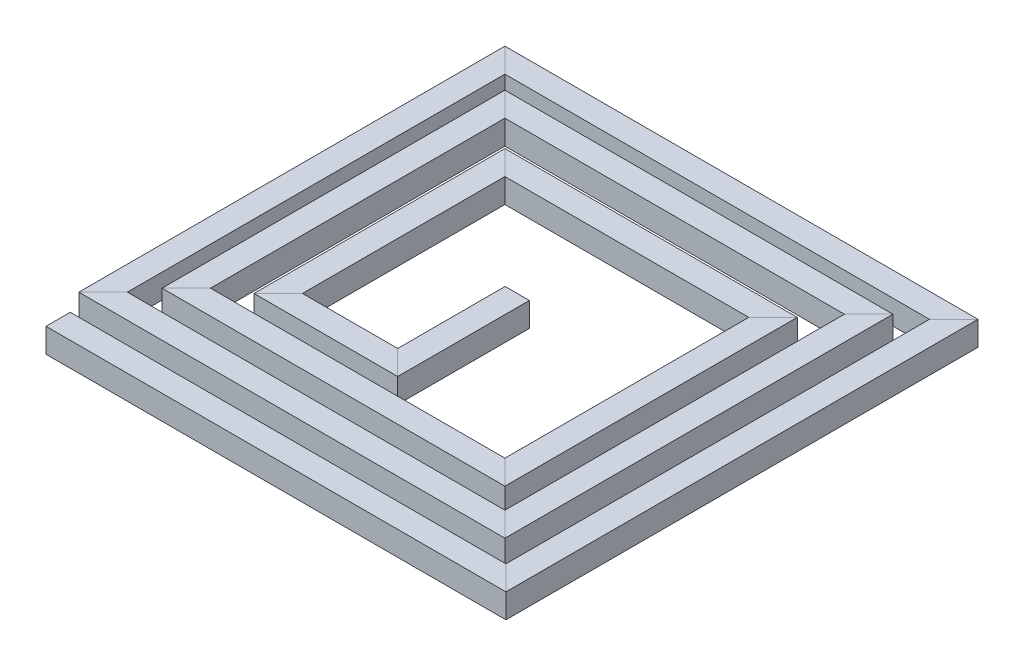
SolidWorks part; units mm, degrees
ref_plane "Front Plane" through (0, 0, 0) normal (0, 0, 1) x (1, 0, 0)
ref_plane "Top Plane" through (0, 0, 0) normal (0, 1, 0) x (1, 0, 0)
ref_plane "Right Plane" through (0, 0, 0) normal (1, 0, 0) x (0, 0, -1)
sketch "Sketch2" plane through (0, 0, 0) normal (0, 1, 0) x (1, 0, 0)
  line L0 (-56.4335, -33.6142) -> (73.6714, -33.6142)
  line L1 (73.6714, -33.6142) -> (73.6714, 96.4907)
  line L2 (73.6714, 96.4907) -> (-56.7311, 96.4907)
  line L3 (-56.7311, 96.4907) -> (-56.7311, -20.2657)
  line L4 (-56.7311, -20.2657) -> (60.0253, -20.2657)
  line L5 (60.0253, -20.2657) -> (60.0253, 85.4121)
  line L6 (60.0253, 85.4121) -> (-45.6525, 85.4121)
  line L7 (-45.6525, 85.4121) -> (-45.6525, -7.1713)
  line L8 (-45.6525, -7.1713) -> (46.9309, -7.1713)
  line L9 (46.9309, -7.1713) -> (46.9309, 70.7291)
  line L10 (46.9309, 70.7291) -> (-30.9695, 70.7291)
  line L11 (-30.9695, 70.7291) -> (-30.9695, 4.8539)
  line L12 (-30.9695, 4.8539) -> (3.7587, 4.8539)
  line L13 (3.7587, 4.8539) -> (3.7587, 39.5821)
  point P2 (3.7587, 6.5481)
  point P16 (-30.9695, 4.8539)
ref_plane "Plane1" through (-56.4335, 0, 0) normal (1, 0, 0) x (0, 0, -1)
sketch "Sketch3" plane through (-56.4335, 0, 0) normal (1, 0, 0) x (0, 0, -1)
  line L0 (-30.0909, -3.5233) -> (-37.1375, -3.5233)
  line L1 (-37.1375, -3.5233) -> (-37.1375, 3.5233)
  line L2 (-37.1375, 3.5233) -> (-30.0909, 3.5233)
  line L3 (-30.0909, 3.5233) -> (-30.0909, -3.5233)
  point P2 (-30.0909, 0)
  point P5 (-33.6142, 3.5233)
sweep "Sweep1" add profiles "Sketch3" path "Sketch2"
